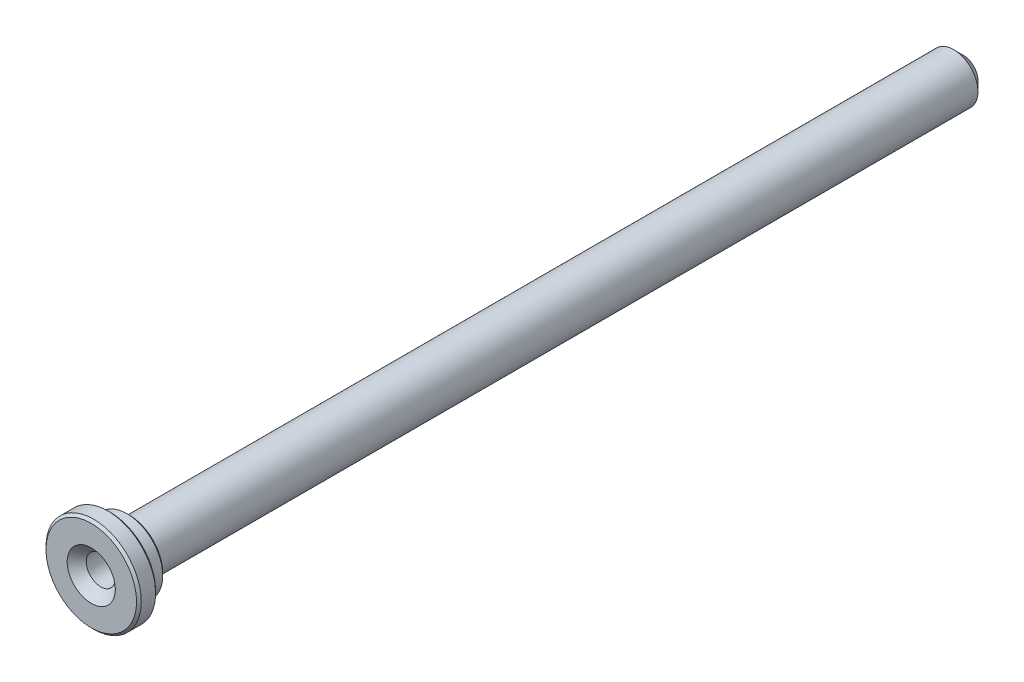
SolidWorks part; units mm, degrees
ref_plane "Спереди" through (0, 0, 0) normal (0, 0, 1) x (1, 0, 0)
ref_plane "Сверху" through (0, 0, 0) normal (0, 1, 0) x (1, 0, 0)
ref_plane "Справа" through (0, 0, 0) normal (1, 0, 0) x (0, 0, -1)
sketch "Эскиз1" plane through (0, 0, 0) normal (1, 0, 0) x (0, 0, -1)
  line L0 (0, 0) -> (-36096.6067, 0) construction
  line L1 (0, 0) -> (0, 5.1)
  line L2 (0, 5.1) -> (-175, 5.1)
  line L3 (-175, 5.1) -> (-175, 7.5)
  line L4 (-175, 7.5) -> (-179, 7.5)
  line L5 (-179, 7.5) -> (-179, 10)
  line L6 (-179, 10) -> (-183, 10)
  line L7 (-183, 10) -> (-183, 3.05)
  line L8 (-183, 3.05) -> (-143, 3.05)
  line L10 (-140.777, 0) -> (0, 0)
  line L11 (-143, 3.05) -> (-140.777, 0)
  dimension "D1" = 10.2
  dimension "D2" = 6.1
  dimension "D3" = 183
  dimension "D4" = 175
  dimension "D5" = 4
  dimension "D6" = 15
  dimension "D7" = 20
  dimension "D8" = 40
revolve "Повернуть1" add sketch "Эскиз1" angle 360 about L0
chamfer "Фаска1" distance 2 angle 45 2 edges at (-5.1, 0, 0) (-3.05, 0, 183)
chamfer "Фаска2" distance 0.5 angle 45 3 edges at (-7.5, 0, 175) (-10, 0, 179) (-10, 0, 183)
